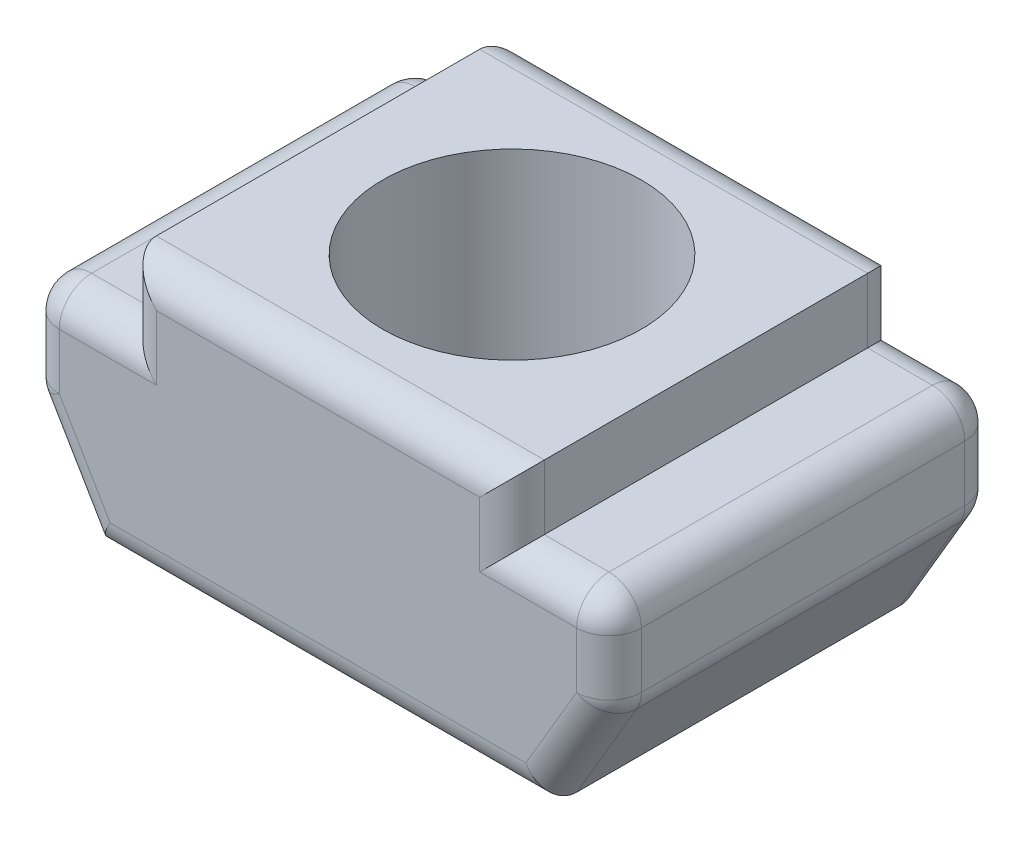
SolidWorks part; units mm, degrees
ref_plane "Alzado" through (0, 0, 0) normal (0, 0, 1) x (1, 0, 0)
ref_plane "Planta" through (0, 0, 0) normal (0, 1, 0) x (1, 0, 0)
ref_plane "Vista lateral" through (0, 0, 0) normal (1, 0, 0) x (0, 0, -1)
sketch "Croquis1" plane through (0, 0, 0) normal (0, 0, 1) x (1, 0, 0)
  line L0 (-4.5, 0) -> (4.5, 0)
  line L1 (0, 0) -> (0, -3.2)
  line L2 (-3.5, -3.2) -> (3.5, -3.2)
  line L5 (-4.5, 0) -> (-4.5, -1.5)
  line L6 (-4.5, -1.5) -> (-3.5, -3.2)
  line L7 (4.5, 0) -> (4.5, -1.5)
  line L8 (4.5, -1.5) -> (3.5, -3.2)
  point P4 (0, 0)
  point P10 (0, -3.2)
  dimension "D1" = 3.2
  dimension "D2" = 7
  dimension "D3" = 1.5
  dimension "D4" = 9
extrude "Saliente-Extruir2" add sketch "Croquis1" along normal blind 6 contours L5 L6 L2 L1 L0 | L8 L7 L0 L1 L2
sketch "Croquis2" plane through (0, 0, 6) normal (0, 0, 1) x (1, 0, 0)
  line L0 (0, -3.2) -> (0, 0) construction
  line L1 (-3.5, -3.2) -> (3.5, -3.2) construction
  line L2 (-4.5, 0) -> (4.5, 0) construction
  line L3 (-3, 1) -> (3, 1)
  line L4 (-3, 1) -> (-3, 0)
  line L5 (-3, 0) -> (3, 0)
  line L6 (3, 1) -> (3, 0)
  line L7 (-3, 1) -> (3, 0) construction
  line L8 (-3, 0) -> (3, 1) construction
  point P5 (0, 0.5)
  dimension "D1" = 1
  dimension "D2" = 6
extrude "Saliente-Extruir3" add sketch "Croquis2" against normal blind 6 contours L4 L3 L6 L5
sketch "Croquis3" plane through (0, 1, 0) normal (0, 1, 0) x (1, 0, 0)
  line L0 (3, -6) -> (-3, 0) construction
  line L1 (-3, 0) -> (-3, -6) construction
  line L2 (-3, -6) -> (3, 0) construction
  circle A0 centre (0, -3) radius 2
  dimension "D1" = 4
extrude "Cortar-Extruir1" cut sketch "Croquis3" against normal through all contours A0
fillet "Redondeo1" radius 0.5 24 edges at (-4, -2.35, 0) (0, -3.2, 0) (4, -2.35, 0) (3.75, 0, 0) (3, 0.5, 6) (3, 0.5, 0) (0, 1, 6) (0, 1, 0) (-3, 0.5, 6) (-3, 0.5, 0) (-3.75, 0, 0) (-4.5, 0, 3) (-4.5, -1.5, 3) (-4.5, -0.75, 0) (4.5, -1.5, 3) (4.5, 0, 3) (4.5, -0.75, 0) (-3.75, 0, 6) (3.75, 0, 6) (4.5, -0.75, 6) (4, -2.35, 6) (0, -3.2, 6) (-4, -2.35, 6) (-4.5, -0.75, 6)
